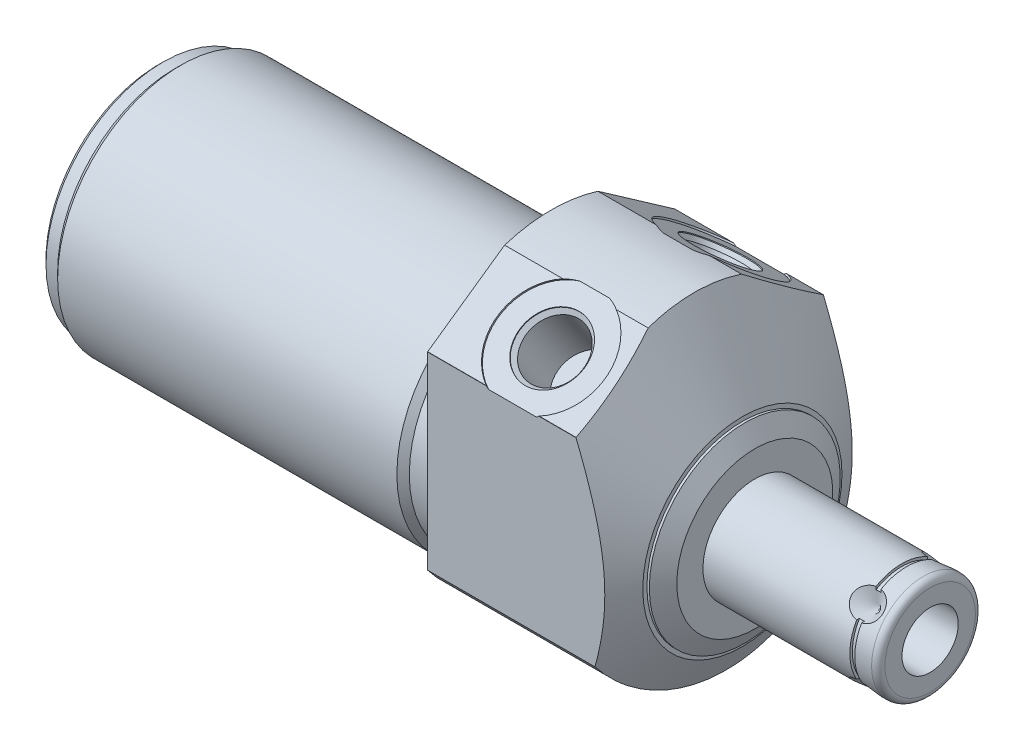
SolidWorks part; units mm, degrees
material "Alloy Steel"
ref_plane "Front Plane" through (0, 0, 0) normal (0, 0, 1) x (1, 0, 0)
ref_plane "Top Plane" through (0, 0, 0) normal (0, 1, 0) x (1, 0, 0)
ref_plane "Right Plane" through (0, 0, 0) normal (1, 0, 0) x (0, 0, -1)
sketch "Sketch1" plane through (0, 0, 0) normal (1, 0, 0) x (0, 0, -1)
  circle A0 centre (0, 0) radius 25.4
  dimension "D1" = 50.8
extrude "Extrude1" add sketch "Sketch1" along normal blind 31.1404 and the other way blind 60.1472
sketch "Sketch2" plane through (0, 0, 0) normal (1, 0, 0) x (0, 0, -1)
  line L0 (-14.6964, -4.191) -> (14.6964, -4.191) construction
  circle A0 centre (0, -4.191) radius 18.8595
  circle A1 centre (0, 0) radius 25.4 construction
  circle A2 centre (0, 0) radius 25.4
  dimension "D1" = 37.719
  dimension "D2" = 4.191
extrude "Cut-Extrude1" cut sketch "Sketch2" against normal up to next
sketch "Sketch4" plane through (31.1404, 0, 0) normal (-1, 0, 0) x (0, 0, 1)
  line L0 (18.923, -14.4553) -> (18.923, 14.4553)
  line L1 (18.9056, 14.4781) -> (7.1389, 22.7172)
  line L2 (-18.923, -14.4553) -> (-18.923, 14.4553)
  line L3 (-18.9056, 14.4781) -> (-7.1389, 22.7172)
  line L4 (0, -20.9029) -> (0, 19.86) construction
  circle A0 centre (0, 0) radius 25.4 construction
  circle A1 centre (0, 0) radius 25.4
  arc A2 (-18.923, -14.4553) -> (18.923, -14.4553) centre (0, 0) ccw
  arc A3 (7.1389, 22.7172) -> (-7.1389, 22.7172) centre (0, 0) ccw
  arc A4 (18.923, 14.4553) -> (18.9056, 14.4781) centre (0, 0) ccw
  arc A6 (-18.9056, 14.4781) -> (-18.923, 14.4553) centre (0, 0) ccw
  dimension "D4" = 23.8125
  dimension "D1" = 37.846
  dimension "D2" = 55
  dimension "D3" = 26.1366
extrude "Cut-Extrude3" cut sketch "Sketch4" along normal up to next
sketch "Sketch6" plane through (0, 0, 0) normal (0, 0, 1) x (1, 0, 0)
  line L0 (16.3822, 33.309) -> (29.2354, 11.0466)
  line L1 (1.9872, -4.191) -> (19.8625, -4.191) construction
  line L2 (-60.1472, -4.191) -> (0, -4.191) construction
  line L4 (31.1404, 7.747) -> (31.1404, 33.309)
  line L5 (31.1404, 33.309) -> (16.3822, 33.309)
  line L7 (29.2354, 11.0466) -> (29.2354, 10.414)
  line L8 (29.2354, 10.414) -> (29.6006, 10.414)
  line L9 (29.6006, 10.414) -> (31.1404, 7.747)
  line L11 (31.1404, -14.4553) -> (31.1404, 14.4553) construction
  dimension "D1" = 23.876
  dimension "D2" = 75
  dimension "D3" = 29.21
  dimension "D4" = 1.905
  dimension "D5" = 30
revolve "Cut-Revolve2" cut sketch "Sketch6" angle 360 about L1
ref_plane "Plane17" through (13.0048, 0, 0) normal (-1, 0, 0) x (0, 0, 1)
sketch "S2D0002" plane through (13.0048, 13.7124, 8.6091) normal (1, 0, 0) x (0, 0.4226, -0.9063)
  line L0 (3.0583, 6.9151) -> (6.2476, 7.4775)
  line L1 (3.0583, 6.9151) -> (3.0804, 6.7901)
  line L2 (3.0804, 6.7901) -> (2.5962, 6.0986)
  line L3 (2.5962, 6.0986) -> (4.1024, -2.4437)
  line L4 (4.1024, -2.4437) -> (-0.25, -3.2112)
  line L5 (-0.25, -3.2112) -> (-1.9261, 6.2942)
  line L6 (1.3861, -12.4899) -> (-0.9428, 0.7176) construction
  line L7 (6.2035, 7.7276) -> (6.2476, 7.4775)
  line L8 (5.1381, 7.5398) -> (-9.0082, 5.0454) construction
  line L9 (6.2035, 7.7276) -> (-1.9261, 6.2942)
  dimension "D1" = 16.51
  dimension "D2" = 0.254
  dimension "D3" = 0.127
  dimension "D4" = 10.033
  dimension "D5" = 45
  dimension "D6" = 8.8392
  dimension "D7" = 9.398
  dimension "D8" = 2.413
revolve "Cut-Revolve3" cut sketch "S2D0002" angle 360 about L6
mirror "Mirror1" about plane through (0, 0, 0) normal (0, 0, 1) of "Cut-Revolve3"
sketch "Sketch10" plane through (0, 0, 0) normal (0, 0, 1) x (1, 0, 0)
  line L0 (0, 14.6685) -> (0, 13.716)
  line L1 (0, 13.716) -> (-3.81, 13.716)
  line L2 (-3.81, 13.716) -> (-4.7625, 14.6685)
  line L3 (-5.094, -4.191) -> (0.2426, -4.191) construction
  line L4 (0, 14.6685) -> (-4.7625, 14.6685)
  line L5 (-60.1472, -4.191) -> (0, -4.191) construction
  line L6 (0, 14.6685) -> (-60.1472, 14.6685) construction
  line L7 (0, 14.4553) -> (0, -14.4553) construction
  dimension "D1" = 35.814
  dimension "D2" = 3.81
  dimension "D3" = 45
revolve "Cut-Revolve6" cut sketch "Sketch10" angle 360 about L3
sketch "Sketch12" plane through (0, 0, 0) normal (0, 0, 1) x (1, 0, 0)
  line L0 (-60.1472, 14.6685) -> (-60.1472, 13.716)
  line L1 (-60.1472, 13.716) -> (-57.6072, 13.716)
  line L2 (-57.6072, 13.716) -> (-56.6547, 14.6685)
  line L3 (-50.9283, -4.191) -> (-48.1063, -4.191) construction
  line L4 (-60.1472, 14.6685) -> (-56.6547, 14.6685)
  line L5 (-60.1472, -4.191) -> (-4.7625, -4.191) construction
  line L6 (-4.7625, 14.6685) -> (-60.1472, 14.6685) construction
  line L7 (-60.1472, 14.6685) -> (-60.1472, -23.0505) construction
  dimension "D1" = 35.814
  dimension "D2" = 2.54
  dimension "D3" = 45
revolve "Cut-Revolve8" cut sketch "Sketch12" angle 360 about L3
chamfer "Chamfer1" distance 0.762 angle 45 1 edges at (-60.1472, -4.191, 17.907)
sketch "Sketch13" plane through (0, 0, 0) normal (0, 0, 1) x (1, 0, 0)
  line L0 (31.1404, -4.191) -> (57.95, -4.191)
  line L1 (57.95, -4.191) -> (57.95, -11.1125)
  line L2 (56.934, -12.1285) -> (31.1404, -12.1285)
  line L3 (31.1404, -12.1285) -> (31.1404, -4.191)
  line L4 (4.7498, -4.191) -> (27.0459, -4.191) construction
  line L5 (-56.6547, -4.191) -> (-4.7625, -4.191) construction
  line L6 (31.1404, -16.129) -> (31.1404, 7.747) construction
  line L7 (0, 14.4553) -> (0, -14.4553) construction
  arc A0 (56.934, -12.1285) -> (57.95, -11.1125) centre (56.934, -11.1125) ccw
  dimension "D2" = 1.016
  dimension "D1" = 57.95
  dimension "D3" = 15.875
revolve "Revolve1" add sketch "Sketch13" angle 360 about L4
ref_plane "Plane18" through (0, -2.0955, -2.0955) normal (0, 0.7071, 0.7071) x (-1, 0, 0)
sketch "S2D0001" plane through (0, 0, 0) normal (0, 0, 1) x (1, 0, 0)
  line L0 (57.95, 0.1143) -> (42.71, 0.1143)
  line L1 (42.71, 0.1143) -> (40.1231, -4.191)
  line L2 (57.95, 0.1143) -> (57.95, -4.191)
  line L3 (57.95, -4.191) -> (40.1231, -4.191)
  line L4 (-2.8067, -4.191) -> (-15.8378, -4.191) construction
  line L5 (56.934, -4.191) -> (31.1404, -4.191) construction
  line L6 (57.95, -11.1125) -> (57.95, 2.7305) construction
  dimension "D1" = 8.6106
  dimension "D2" = 15.24
  dimension "D3" = 59
revolve "Cut-Revolve9" cut sketch "S2D0001" angle 360 about L4
sketch "Sketch16" plane through (0, -7.1545, 2.9635) normal (0, -0.7071, -0.7071) x (1, 0, 0)
  line L0 (53.9876, -12.1285) -> (51.5746, -12.1285)
  line L1 (51.5746, -12.1285) -> (53.9876, -9.7155)
  line L2 (53.9876, -12.1285) -> (53.9876, -9.7155)
  line L3 (53.9876, -3.4788) -> (53.9876, 0.0794) construction
  line L4 (57.95, -11.1125) -> (57.95, 2.7305) construction
  line L5 (31.1404, -12.1285) -> (56.934, -12.1285) construction
  dimension "D1" = 3.9624
  dimension "D2" = 4.826
  dimension "D3" = 45
revolve "Cut-Revolve10" cut sketch "Sketch16" angle 360 about L3
pattern_circular "CirPattern1" count 4 over 360 about axis through (4.7498, -4.191, 0) along (-1, 0, 0) of "Cut-Revolve10"
sketch "Sketch21" plane through (0, 0, 0) normal (0, 0, 1) x (1, 0, 0)
  line L1 (53.6066, 3.7465) -> (54.3686, 3.7465)
  line L2 (53.6066, 3.7465) -> (53.6066, 3.3655)
  line L3 (53.6066, 3.3655) -> (54.3686, 3.3655)
  line L4 (54.3686, 3.7465) -> (54.3686, 3.3655)
  line L5 (53.9876, -0.7782) -> (53.9876, 2.3032) construction
  line L7 (23.8735, -4.191) -> (50.6625, -4.191) construction
  line L10 (57.95, -11.1125) -> (57.95, 2.7305) construction
  line L11 (61.4287, -4.191) -> (47.9446, -4.191) construction
  dimension "D1" = 0.381
  dimension "D2" = 0.762
  dimension "D3" = 3.5814
  dimension "D4" = 7.9375
revolve "Cut-Revolve11" cut sketch "Sketch21" angle 360 about L7
